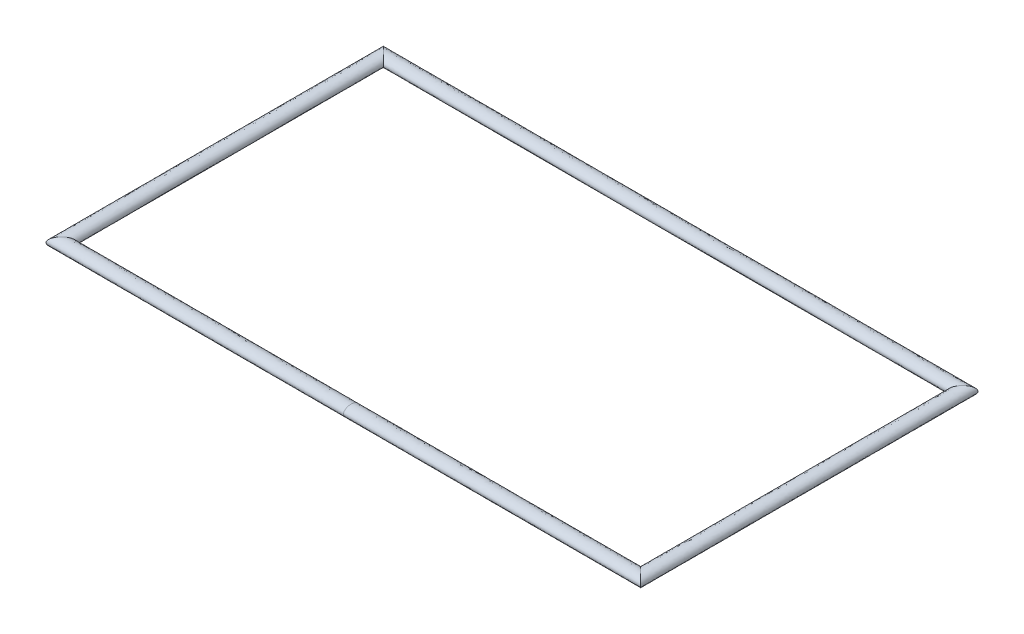
SolidWorks part; units mm, degrees
ref_plane "Ebene vorne" through (0, 0, 0) normal (0, 0, 1) x (1, 0, 0)
ref_plane "Ebene oben" through (0, 0, 0) normal (0, 1, 0) x (1, 0, 0)
ref_plane "Ebene rechts" through (0, 0, 0) normal (1, 0, 0) x (0, 0, -1)
sketch "Skizze2" plane through (0, 0, 0) normal (0, 1, 0) x (1, 0, 0)
  line L5 (-43.2, -24) -> (43.2, -24)
  line L6 (-43.2, -24) -> (-43.2, 24)
  line L11 (-43.2, 24) -> (43.2, 24)
  line L12 (43.2, -24) -> (43.2, 24)
  line L13 (-43.2, -24) -> (43.2, 24) construction
  line L14 (-43.2, 24) -> (43.2, -24) construction
  point P0 (0, 0)
  dimension "D1" = 48
  dimension "D2" = 86.4
sketch "Skizze9" plane through (0, 0, 0) normal (1, 0, 0) x (0, 0, -1)
  line L0 (-24, 0) -> (24, 0) construction
  line L1 (24, 0) -> (-24, 0) construction
  ellipse E0 centre (-24, 0) end of major axis (-22.85, 0) minor radius 0.75
  dimension "D1" = 2.3
  dimension "D2" = 1.5
sweep "Austragung2" add profiles "Skizze9" path "Skizze2"
